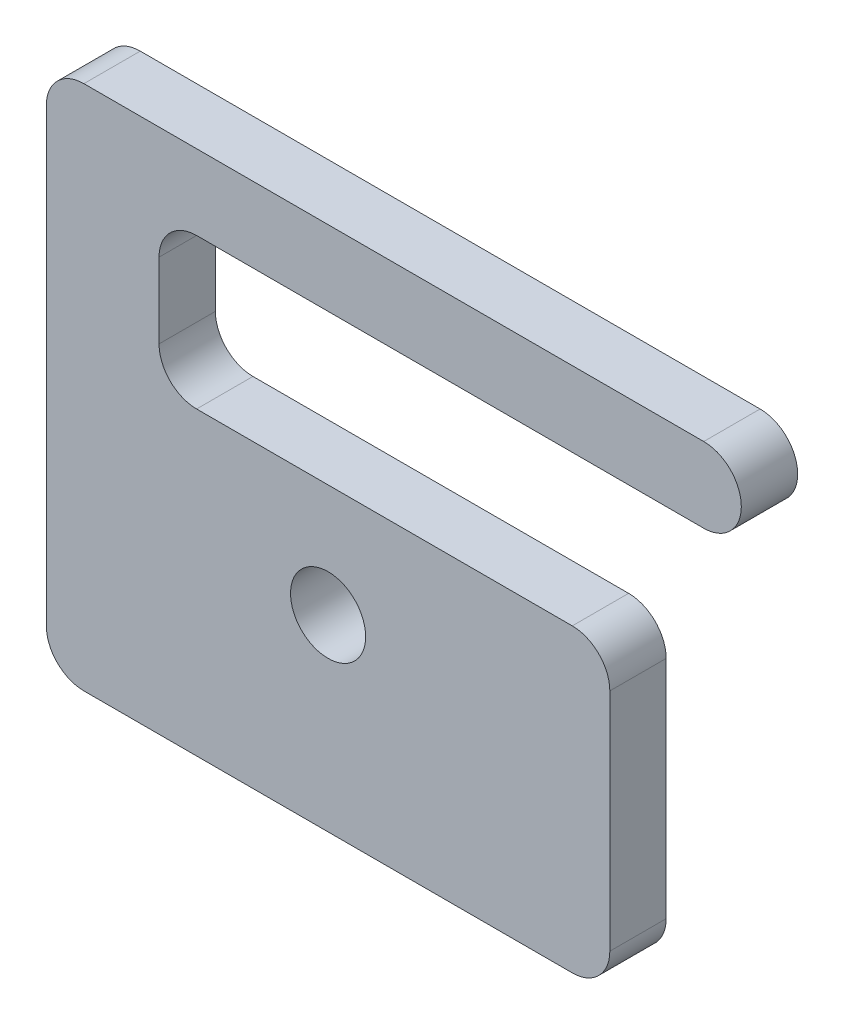
SolidWorks part; units mm, degrees
material "1.1221 (C60E)"
ref_plane "Plan de face" through (0, 0, 0) normal (0, 0, 1) x (1, 0, 0)
ref_plane "Plan de dessus" through (0, 0, 0) normal (0, 1, 0) x (1, 0, 0)
ref_plane "Plan de droite" through (0, 0, 0) normal (1, 0, 0) x (0, 0, -1)
sketch "Esquisse1" plane through (0, 0, 0) normal (0, 0, 1) x (1, 0, 0)
  line L0 (0.75, 0.2) -> (0.75, -0.4)
  line L1 (-0.65, 0.9) -> (1, 0.9)
  line L2 (-0.75, 0.8) -> (-0.75, -0.4)
  line L3 (-0.65, -0.5) -> (0.65, -0.5)
  line L5 (-0.35, 0.7) -> (1, 0.7)
  line L6 (-0.45, 0.6) -> (-0.45, 0.4)
  line L7 (-0.35, 0.3) -> (0.65, 0.3)
  line L9 (0, 0) -> (0, 0.5967) construction
  line L10 (0.325, 0.7) -> (0.325, 0.9) construction
  circle A0 centre (0, 0) radius 0.1
  arc A1 (1, 0.7) -> (1, 0.9) centre (1, 0.8) ccw
  arc A2 (-0.45, 0.4) -> (-0.35, 0.3) centre (-0.35, 0.4) ccw
  arc A3 (-0.35, 0.7) -> (-0.45, 0.6) centre (-0.35, 0.6) ccw
  arc A4 (0.65, 0.3) -> (0.75, 0.2) centre (0.65, 0.2) cw
  arc A5 (0.65, -0.5) -> (0.75, -0.4) centre (0.65, -0.4) ccw
  arc A6 (-0.75, -0.4) -> (-0.65, -0.5) centre (-0.65, -0.4) ccw
  arc A7 (-0.65, 0.9) -> (-0.75, 0.8) centre (-0.65, 0.8) ccw
  point P15 (-0.45, 0.3)
  point P18 (-0.45, 0.7)
  point P23 (0.75, -0.5)
  point P26 (-0.75, -0.5)
  point P31 (0.325, 0.9)
  dimension "D1" = 0.2
  dimension "D9" = 0.1
  dimension "D2" = 1.5
  dimension "D3" = 0.5
  dimension "D4" = 0.3
  dimension "D5" = 0.4
  dimension "D6" = 0.3
  dimension "D7" = 0.2
  dimension "D8" = 1
extrude "Boss.-Extru.1" add sketch "Esquisse1" against normal blind 0.15
